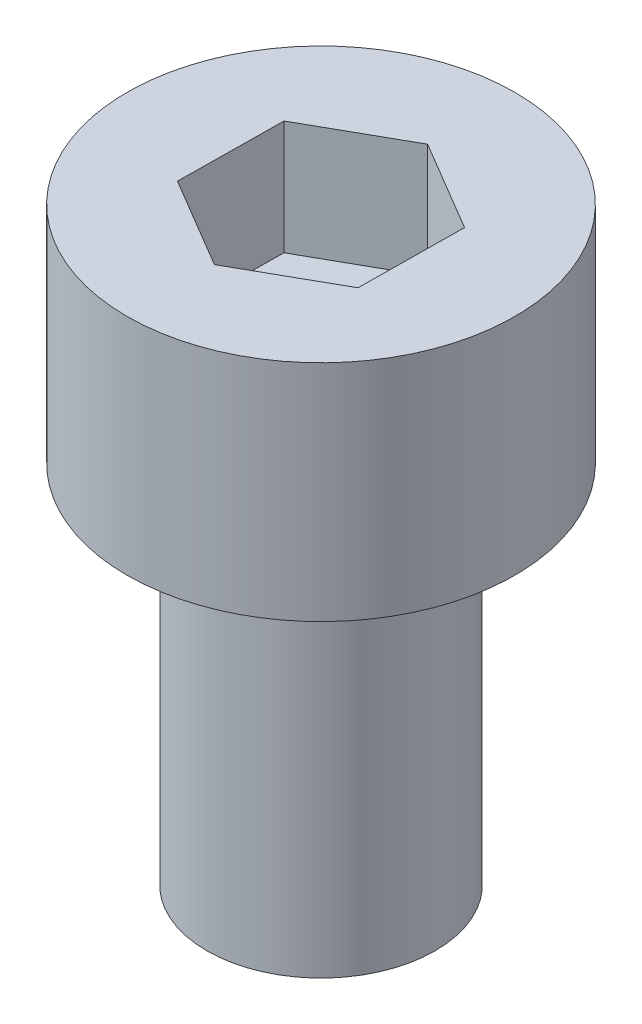
SolidWorks part; units mm, degrees
ref_plane "前视基准面" through (0, 0, 0) normal (0, 0, 1) x (1, 0, 0)
ref_plane "上视基准面" through (0, 0, 0) normal (0, 1, 0) x (1, 0, 0)
ref_plane "右视基准面" through (0, 0, 0) normal (1, 0, 0) x (0, 0, -1)
sketch "草图1" plane through (0, 0, 0) normal (0, 1, 0) x (1, 0, 0)
  circle A0 centre (0, 0) radius 2.5
  dimension "D1" = 5
extrude "凸台-拉伸1" add sketch "草图1" along normal blind 8
sketch "草图2" plane through (0, 8, 0) normal (0, 1, 0) x (1, 0, 0)
  circle A0 centre (0, 0) radius 4.25
  dimension "D1" = 8.5
extrude "凸台-拉伸2" add sketch "草图2" along normal blind 4.91
sketch "草图3" plane through (0, 12.91, 0) normal (0, 1, 0) x (1, 0, 0)
  line L1 (1.9872, -1.1765) -> (2.0125, 1.1327)
  line L2 (2.0125, 1.1327) -> (0.0253, 2.3093)
  line L3 (0.0253, 2.3093) -> (-1.9872, 1.1765)
  line L4 (-1.9872, 1.1765) -> (-2.0125, -1.1327)
  line L5 (-2.0125, -1.1327) -> (-0.0253, -2.3093)
  line L6 (-0.0253, -2.3093) -> (1.9872, -1.1765)
  circle A0 centre (0, 0) radius 2 construction
  dimension "D1" = 4
extrude "切除-拉伸1" cut sketch "草图3" against normal blind 2.5
